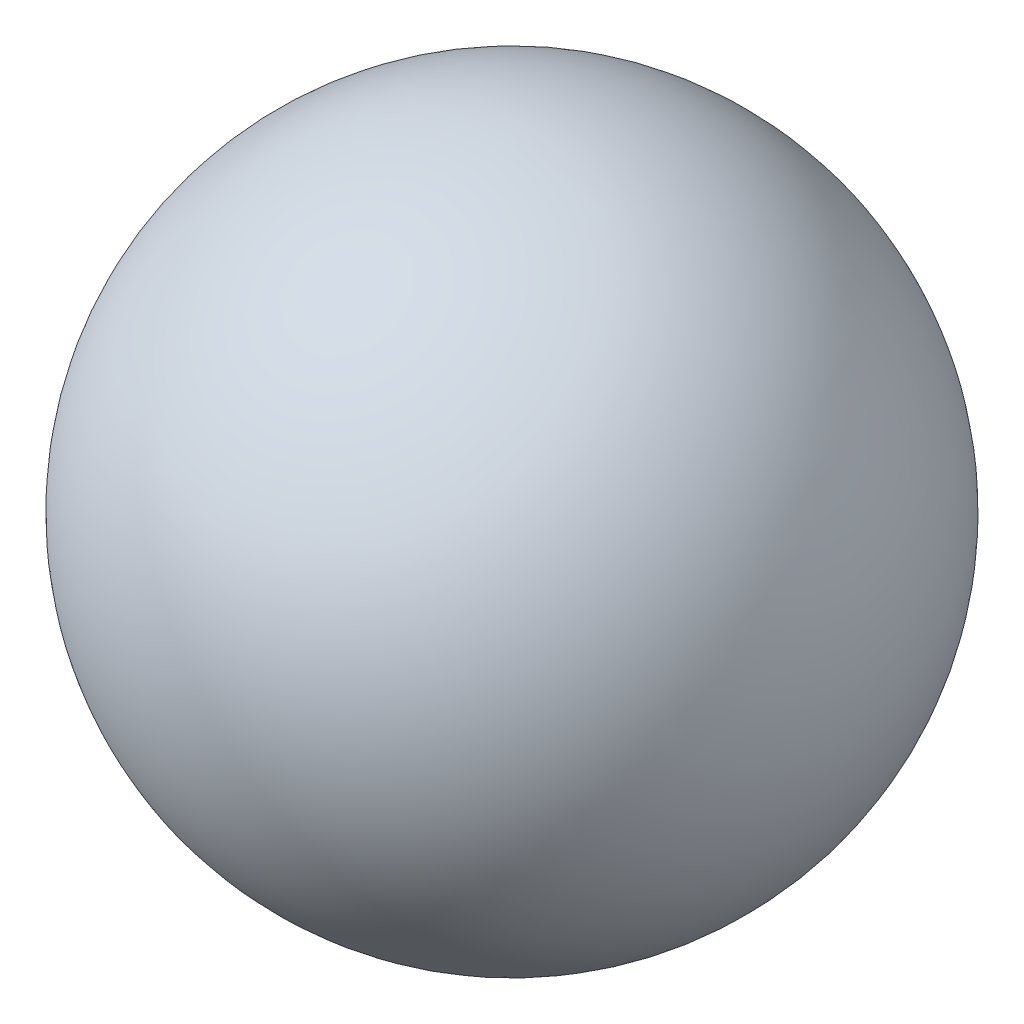
SolidWorks part; units mm, degrees
ref_plane "Front Plane" through (0, 0, 0) normal (0, 0, 1) x (1, 0, 0)
ref_plane "Top Plane" through (0, 0, 0) normal (0, 1, 0) x (1, 0, 0)
ref_plane "Right Plane" through (0, 0, 0) normal (1, 0, 0) x (0, 0, -1)
sketch "Sketch1" plane through (0, 0, 0) normal (0, 1, 0) x (1, 0, 0)
  line L0 (0, 76.2) -> (0, -76.2)
  arc A0 (0, -76.2) -> (0, 76.2) centre (0, 0) ccw
  point P6 (0, 0)
  dimension "D1" = 152.4
revolve "Revolve1" add sketch "Sketch1" angle 360 about L0
